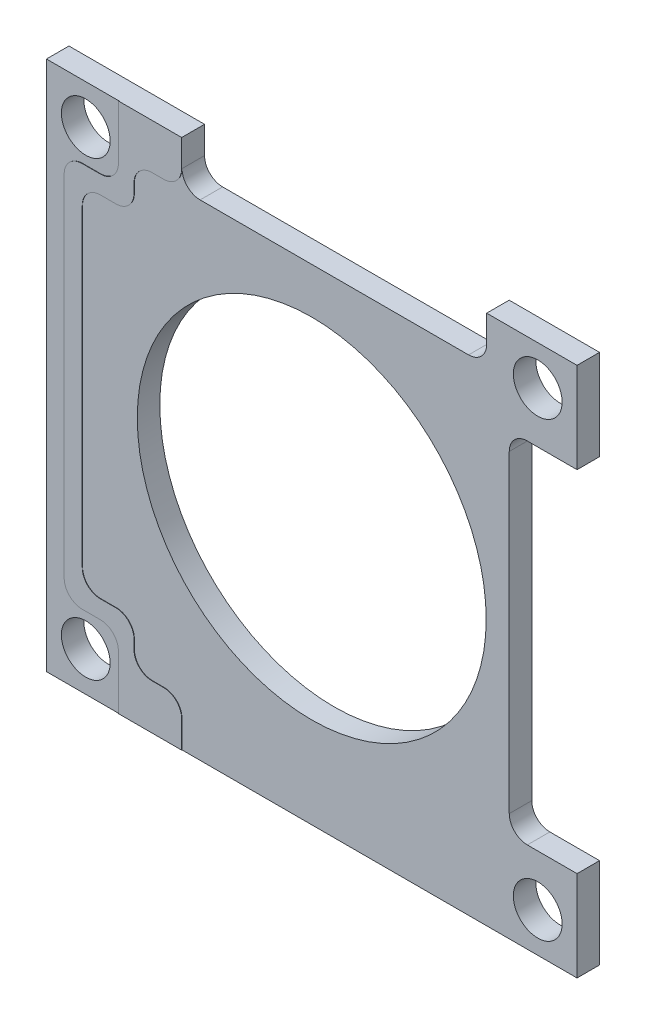
SolidWorks part; units mm, degrees
ref_plane "Front Plane" through (0, 0, 0) normal (0, 0, 1) x (1, 0, 0)
ref_plane "Top Plane" through (0, 0, 0) normal (0, 1, 0) x (1, 0, 0)
ref_plane "Right Plane" through (0, 0, 0) normal (1, 0, 0) x (0, 0, -1)
sketch "Sketch1" plane through (0, 0, 0) normal (0, 0, 1) x (1, 0, 0)
  line L1 (-37.2745, 37.2745) -> (37.2745, 37.2745)
  line L2 (-37.2745, 37.2745) -> (-37.2745, -37.2745)
  line L3 (-37.2745, -37.2745) -> (37.2745, -37.2745)
  line L4 (37.2745, 37.2745) -> (37.2745, -37.2745)
  circle A0 centre (0, 0) radius 24.511
  dimension "D5" = 49.022
  dimension "D1" = 74.549
  dimension "D2" = 74.549
  dimension "D3" = 37.2745
  dimension "D4" = 37.2745
extrude "Boss-Extrude1" add sketch "Sketch1" along normal blind 1.5748 and the other way blind 1.5875
sketch "Sketch2" plane through (0, 0, 1.5748) normal (0, 0, 1) x (1, 0, 0)
  line L0 (0, 25.7973) -> (0, -24.2806) construction
  line L1 (-23.5201, 0) -> (29.7887, 0) construction
  line L2 (0, 0) -> (-59.488, 59.488) construction
  circle A0 centre (-31.75, 31.75) radius 3.429
  dimension "D3" = 6.858
  dimension "D1" = 45
  dimension "D2" = 31.75
extrude "Cut-Extrude1" cut sketch "Sketch2" against normal through all
sketch "Sketch20" plane through (0, 0, 1.5748) normal (0, 0, 1) x (1, 0, 0)
  line L0 (-24.9212, 24.5745) -> (-24.9212, 30.9245)
  line L1 (-27.1145, 37.2745) -> (-27.1145, 27.1145)
  line L2 (37.2745, 37.2745) -> (-37.2745, 37.2745) construction
  line L3 (-27.1145, 27.1145) -> (-34.7345, 27.1145)
  line L4 (-34.7345, 27.1145) -> (-34.7345, 0)
  line L5 (-34.7345, 0) -> (-32.1945, 0)
  line L6 (-32.1945, 0) -> (-32.1945, 24.5745)
  line L7 (-32.1945, 24.5745) -> (-24.9212, 24.5745)
  line L8 (-24.9212, 30.9245) -> (-18.2245, 30.9245)
  line L9 (-18.2245, 37.2745) -> (-27.1145, 37.2745)
  line L10 (-37.2745, 37.2745) -> (-37.2745, -37.2745) construction
  line L11 (-18.2245, 30.9245) -> (-18.2245, 37.2745)
  dimension "D1" = 2.54
  dimension "D2" = 2.54
  dimension "D3" = 2.54
  dimension "D4" = 10.16
  dimension "D5" = 6.35
  dimension "D6" = 10.16
extrude "Boss-Extrude2" add sketch "Sketch20" along normal blind 0.0508
fillet "Fillet3" radius 2.54 5 edges at (-34.7345, 27.1145, 1.6002) (-32.1945, 24.5745, 1.6002) (-18.2245, 30.9245, 1.6002) (-24.9212, 24.5745, 1.6002) (-24.9212, 30.9245, 1.6002)
mirror "Mirror3" about plane through (0, 0, 0) normal (0, 1, 0) of "Boss-Extrude2", "Fillet3"
mirror "Mirror1" about plane through (0, 0, 0) normal (1, 0, 0) of "Cut-Extrude1"
mirror "Mirror2" about plane through (0, 0, 0) normal (0, 1, 0) of "Mirror1", "Cut-Extrude1"
sketch "Sketch14" plane through (0, 0, 1.5748) normal (0, 0, 1) x (1, 0, 0)
  line L0 (-37.2745, 37.2745) -> (-37.2745, -37.2745) construction
  line L1 (-18.2245, 39.215) -> (24.5745, 39.215)
  line L2 (-18.2245, 39.215) -> (-18.2245, 30.9245)
  line L3 (-18.2245, 30.9245) -> (24.5745, 30.9245)
  line L4 (24.5745, 39.215) -> (24.5745, 30.9245)
  line L6 (37.2745, 37.2745) -> (-18.2245, 37.2745) construction
  line L7 (37.2745, -37.2745) -> (37.2745, 37.2745) construction
  dimension "D1" = 19.05
  dimension "D2" = 12.7
  dimension "D3" = 6.35
extrude "Cut-Extrude2" cut sketch "Sketch14" against normal through all
fillet "Fillet1" radius 2.54 2 edges at (-18.2245, 30.9245, -0.0064) (24.5745, 30.9245, -0.0064)
sketch "Sketch17" plane through (0, 0, 1.5748) normal (0, 0, 1) x (1, 0, 0)
  line L0 (37.2745, 37.2745) -> (24.5745, 37.2745) construction
  line L1 (42.0648, 24.5745) -> (27.7495, 24.5745)
  line L2 (42.0648, 24.5745) -> (42.0648, -24.5745)
  line L3 (42.0648, -24.5745) -> (27.7495, -24.5745)
  line L4 (27.7495, 24.5745) -> (27.7495, -24.5745)
  line L5 (-37.2745, -37.2745) -> (-27.1145, -37.2745) construction
  line L7 (37.2745, -37.2745) -> (37.2745, 37.2745) construction
  dimension "D1" = 12.7
  dimension "D2" = 12.7
  dimension "D3" = 9.525
extrude "Cut-Extrude3" cut sketch "Sketch17" against normal through all
fillet "Fillet2" radius 2.54 2 edges at (27.7495, 24.5745, -0.0064) (27.7495, -24.5745, -0.0064)
fillet "Fillet5" radius 2.54 2 edges at (-27.1145, -27.1145, 1.6002) (-27.1145, 27.1145, 1.6002)
hole_wizard "CSK for #0 Flat Head Machine Screw (100)1" positions "Sketch22" profile "Sketch21" countersink size "#0" standard "ANSI Inch"
sketch "Sketch22" plane through (0, 0, -1.5875) normal (0, 0, -1) x (-1, 0, 0)
  point P0 (19.05, 27.94)
  point P4 (-19.05, -27.94)
  dimension "D1" = 19.05
  dimension "D2" = 27.94
  dimension "D3" = 27.94
  dimension "D4" = 19.05
sketch "Sketch21" plane through (-19.05, 27.94, -1.5875) normal (1, 0, 0) x (0, 1, 0)
  line L0 (0, 0) -> (0, 3.2131)
  line L1 (0, 3.2131) -> (0.889, 3.2131)
  line L2 (0.889, 3.2131) -> (0.889, 0.5222)
  line L3 (0.889, 0.5222) -> (1.5113, 0)
  line L5 (1.5113, 0) -> (0, 0)
  line L6 (-0.889, 0.5222) -> (-1.5113, 0) construction
  line L11 (0, -6.35) -> (0, 107.95) construction
  dimension "Thru Hole Dia." = 1.778
  dimension "Thru Hole Depth" = 3.2131
  dimension "Near C'Sink Dia." = 3.0226
  dimension "Near C'Sink Angle" = 100
hole_wizard "CBORE for #2 Button Head Cap Screw2" positions "Sketch26" profile "Sketch25" counterbore size "#2" standard "ANSI Inch"
sketch "Sketch26" plane through (0, 0, -1.5875) normal (0, 0, -1) x (-1, 0, 0)
  point P0 (-19.05, 27.94)
  point P2 (19.05, -27.94)
  dimension "D1" = 19.05
  dimension "D2" = 27.94
  dimension "D3" = 19.05
  dimension "D4" = 27.94
sketch "Sketch25" plane through (19.05, 27.94, -1.5875) normal (1, 0, 0) x (0, 1, 0)
  line L0 (0, 0) -> (0, 3.2131)
  line L1 (0, 3.2131) -> (1.2192, 3.2131)
  line L3 (1.2192, 3.2131) -> (1.2192, 1.27)
  line L4 (1.2192, 1.27) -> (2.5794, 1.27)
  line L5 (2.5794, 1.27) -> (2.5794, 0)
  line L7 (2.5794, 0) -> (0, 0)
  line L11 (0, -6.35) -> (0, 107.95) construction
  dimension "Thru Hole Dia." = 2.4384
  dimension "Thru Hole Depth" = 3.2131
  dimension "C'Bore Dia." = 5.1587
  dimension "C'Bore Depth" = 1.27
equation "\"D4@Sketch1\"=\"D1@Sketch1\"/2"
equation "\"D3@Sketch1\"=\"D2@Sketch1\"/2"
equation "\"D2@Sketch1\"=\"D1@Sketch1\""
equation "\"D2@Sketch17\"=\"D1@Sketch17\""
equation "\"D3@Sketch22\"=\"D2@Sketch22\""
equation "\"D4@Sketch22\"=\"D1@Sketch22\""
equation "\"D3@Sketch26\"=\"D1@Sketch26\""
equation "\"D4@Sketch26\"=\"D2@Sketch26\""
